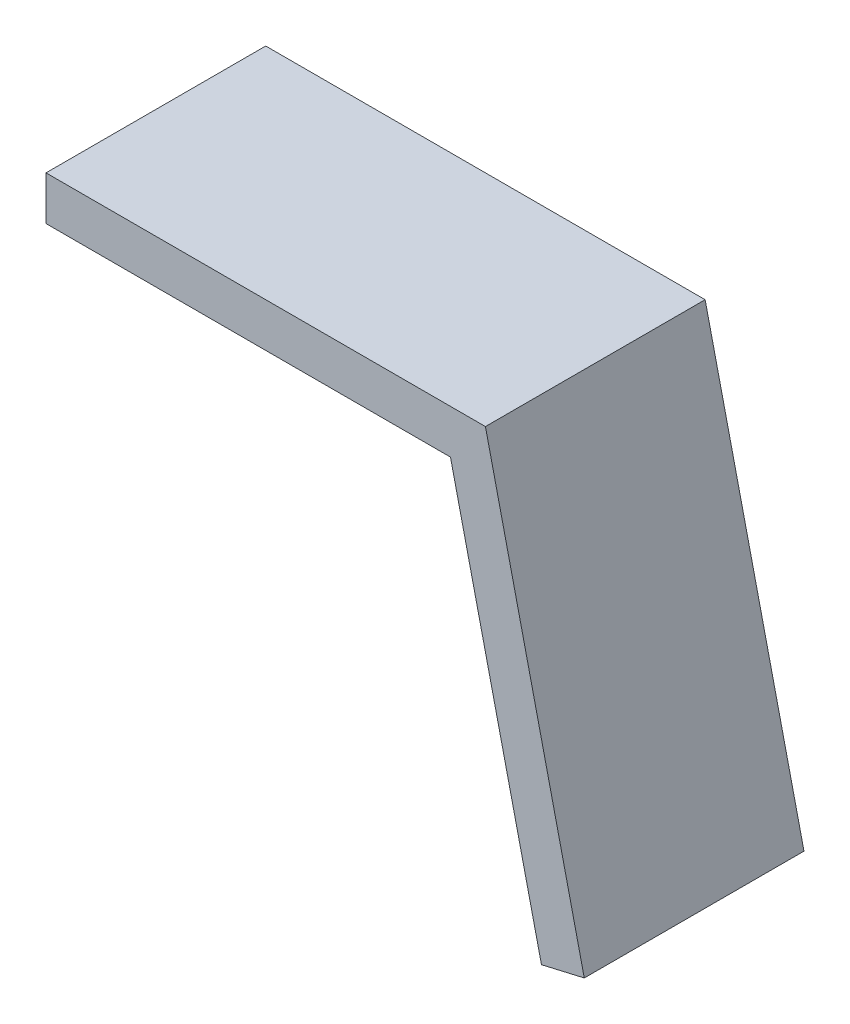
SolidWorks part; units mm, degrees
ref_plane "Front Plane" through (0, 0, 0) normal (0, 0, 1) x (1, 0, 0)
ref_plane "Top Plane" through (0, 0, 0) normal (0, 1, 0) x (1, 0, 0)
ref_plane "Right Plane" through (0, 0, 0) normal (1, 0, 0) x (0, 0, -1)
sketch "Sketch1" plane through (0, 0, 0) normal (0, 0, 1) x (1, 0, 0)
  line L0 (100, 0) -> (0, 0)
  line L1 (100, 0) -> (122.4951, -97.437)
  line L2 (122.4951, -97.437) -> (112.7514, -99.6865)
  line L3 (112.7514, -99.6865) -> (92.0456, -10)
  line L4 (92.0456, -10) -> (0, -10)
  line L5 (0, 0) -> (0, -10)
  dimension "D1" = 103
  dimension "D2" = 10
  dimension "D3" = 10
  dimension "D4" = 100
  dimension "D5" = 100
extrude "Boss-Extrude1" add sketch "Sketch1" along normal blind 50
